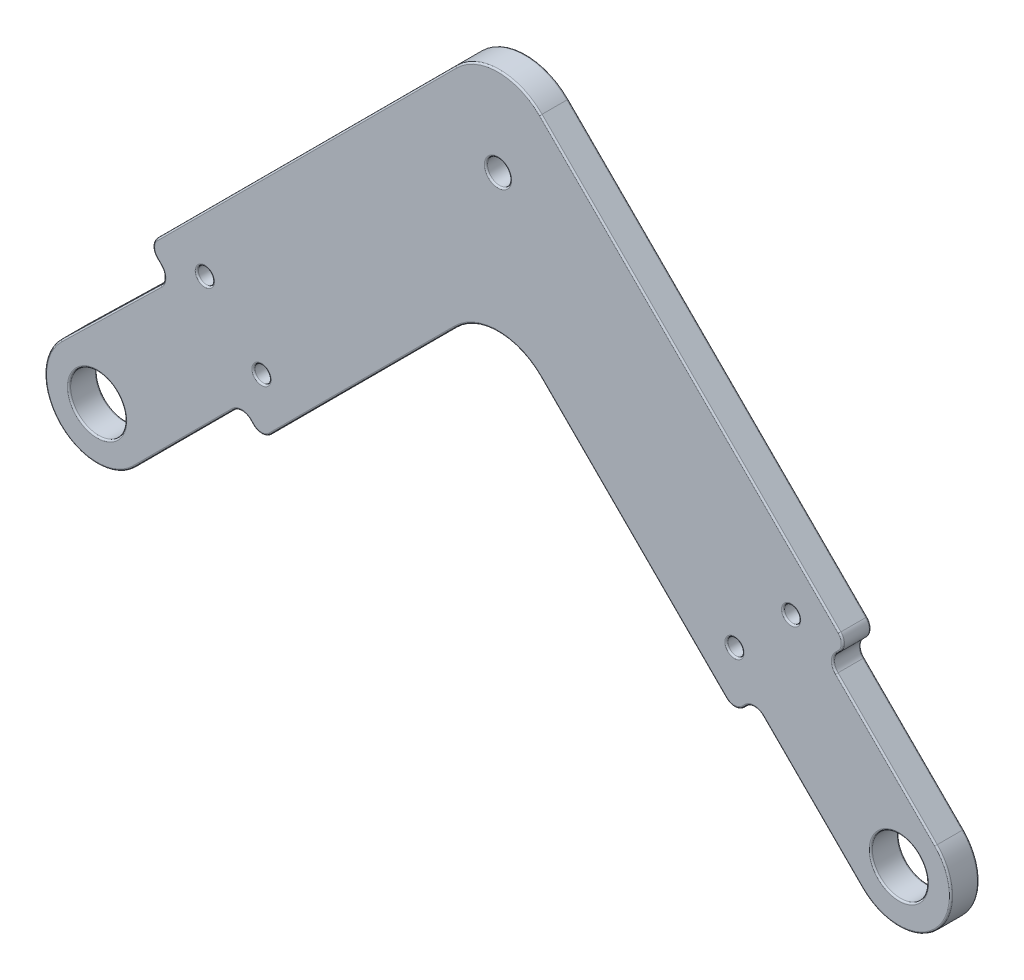
SolidWorks part; units mm, degrees
ref_plane "Front Plane" through (0, 0, 0) normal (0, 0, 1) x (1, 0, 0)
ref_plane "Top Plane" through (0, 0, 0) normal (0, 1, 0) x (1, 0, 0)
ref_plane "Right Plane" through (0, 0, 0) normal (1, 0, 0) x (0, 0, -1)
sketch "Sketch1" plane through (0, 0, 0) normal (0, 0, 1) x (1, 0, 0)
  line L0 (-100, 0) -> (100, 0) construction
  line L1 (-100, 0) -> (0, 100) construction
  line L2 (0, 100) -> (100, 0) construction
  line L3 (0, 0) -> (-50, 50) construction
  line L4 (-40, 60) -> (40, 60) construction
  line L5 (0, 100) -> (0, 60) construction
  circle A0 centre (-100, 0) radius 20
  circle A1 centre (0, 0) radius 20
  circle A2 centre (100, 0) radius 20
  point P2 (0, 0)
  dimension "D5" = 40
  dimension "D1" = 200
  dimension "D2" = 90
  dimension "D3" = 90
  dimension "D4" = 80
sketch "Sketch2" plane through (0, 0, 0) normal (0, 0, 1) x (1, 0, 0)
  line L0 (93.636, 20.5061) -> (79.4939, 6.364)
  line L1 (90.9809, 17.8509) -> (104.534, 4.6576)
  line L2 (-57.0711, 42.9289) -> (-40, 60) construction
  line L3 (-100, 0) -> (0, 100) construction
  line L4 (-40, 60) -> (40, 60) construction
  line L5 (40, 60) -> (86.565, 13.435) construction
  line L6 (0, 100) -> (100, 0) construction
  line L7 (-50, 35.8579) -> (-35.8579, 50)
  line L8 (-35.8579, 50) -> (35.8579, 50)
  line L9 (35.8579, 50) -> (79.4939, 6.364)
  line L10 (-64.1421, 50) -> (-44.1421, 70)
  line L11 (-44.1421, 70) -> (44.1421, 70)
  line L12 (44.1421, 70) -> (93.636, 20.5061)
  line L13 (-64.1421, 50) -> (-50, 35.8579)
  line L14 (82.1491, 9.0191) -> (95.3424, -4.534)
  line L15 (90.1005, 24.0416) -> (75.9584, 9.8995) construction
  line L17 (0, 100) -> (0, 60) construction
  line L18 (6, 70) -> (3.4304, 82.6944)
  line L19 (-6, 70) -> (-3.4304, 82.6944)
  circle A0 centre (100, 0) radius 3.5
  circle A1 centre (100, 0) radius 10 construction
  arc A2 (95.3424, -4.534) -> (104.534, 4.6576) centre (100, 0) ccw
  circle A3 centre (100, 0) radius 20 construction
  circle A4 centre (100, 0) radius 6.5 construction
  circle A5 centre (86.565, 20.5061) radius 1
  circle A6 centre (79.4939, 13.435) radius 1
  circle A7 centre (0, 60) radius 1.5
  circle A9 centre (0, 82) radius 1.5
  arc A10 (3.4304, 82.6944) -> (-3.4304, 82.6944) centre (0, 82) ccw
  circle A11 centre (0, 82) radius 3.5 construction
  circle A13 centre (-50, 50) radius 1.5
  dimension "D4" = 20
  dimension "D5" = 7
  dimension "D9" = 2
  dimension "D12" = 3
  dimension "D18" = 3
  dimension "D3" = 20
  dimension "D7" = 19
  dimension "D8" = 5
  dimension "D10" = 5
  dimension "D11" = 5
  dimension "D13" = 12
  dimension "D15" = 6
  dimension "D16" = 6
  dimension "D1" = 10
  dimension "D2" = 10
  dimension "D6" = 3
  dimension "D14" = 2
sketch "Sketch3" plane through (0, 0, 0) normal (0, 0, 1) x (1, 0, 0)
  line L0 (-86.565, 13.435) -> (-50, 50) construction
  line L1 (-100, 0) -> (0, 100) construction
  line L2 (-50, 50) -> (-13.435, 13.435) construction
  line L3 (0, 0) -> (-50, 50) construction
  line L4 (-79.4939, 6.364) -> (-50, 35.8579)
  line L5 (-50, 35.8579) -> (-20.5061, 6.364)
  line L6 (-93.636, 20.5061) -> (-50, 64.1421)
  line L7 (-50, 64.1421) -> (-6.364, 20.5061)
  line L8 (-79.4939, 6.364) -> (-50, 35.8579) construction
  line L9 (-93.636, 20.5061) -> (-50, 64.1421) construction
  line L10 (-93.636, 20.5061) -> (-79.4939, 6.364)
  line L11 (-6.364, 20.5061) -> (-20.5061, 6.364)
  line L12 (-104.534, 4.6576) -> (-90.9809, 17.8509)
  line L13 (-95.4038, -4.5962) -> (-81.9688, 8.8388)
  line L14 (4.5962, 4.5962) -> (-8.8388, 18.0312)
  line L15 (-4.5962, -4.5962) -> (-18.0312, 8.8388)
  line L16 (-90.1005, 24.0416) -> (-75.9584, 9.8995) construction
  line L17 (-9.8995, 24.0416) -> (-24.0416, 9.8995) construction
  circle A0 centre (-100, 0) radius 3.5
  circle A1 centre (0, 0) radius 3.5
  circle A2 centre (-100, 0) radius 10 construction
  circle A3 centre (0, 0) radius 10 construction
  arc A4 (-104.534, 4.6576) -> (-95.4038, -4.5962) centre (-100, 0) ccw
  arc A5 (-4.5962, -4.5962) -> (4.5962, 4.5962) centre (0, 0) ccw
  circle A6 centre (-100, 0) radius 20 construction
  circle A7 centre (-100, 0) radius 6.5 construction
  circle A8 centre (0, 0) radius 6.5 construction
  circle A9 centre (-86.565, 20.5061) radius 1
  circle A10 centre (-79.4939, 13.435) radius 1
  circle A11 centre (-20.5061, 13.435) radius 1
  circle A12 centre (-13.435, 20.5061) radius 1
  circle A13 centre (-50, 50) radius 1.5 construction
  circle A14 centre (-50, 50) radius 1.5
  dimension "D1" = 7
  dimension "D2" = 20
  dimension "D3" = 3
  dimension "D8" = 2
  dimension "D6" = 19
  dimension "D7" = 19
  dimension "D9" = 5
  dimension "D10" = 5
  dimension "D11" = 5
  dimension "D12" = 5
  dimension "D13" = 5
  dimension "D14" = 5
  dimension "D4" = 10
  dimension "D5" = 10
sketch "Sketch5" plane through (0, 0, 0) normal (0, 0, 1) x (1, 0, 0)
  line L6 (4, 60) -> (4, 70)
  line L7 (-4, 60) -> (-4, 70)
  line L10 (-57.5, 93.3579) -> (57.5, 93.3579)
  line L11 (57.5, 93.3579) -> (57.5, 83.3579)
  line L12 (57.5, 83.3579) -> (44.1421, 70)
  line L13 (44.1421, 70) -> (-44.1421, 70)
  line L14 (-44.1421, 70) -> (-57.5, 83.3579)
  line L15 (-57.5, 83.3579) -> (-57.5, 93.3579)
  line L16 (-22.5, 84.8579) -> (22.5, 84.8579) construction
  line L17 (-22.5, 89.3579) -> (22.5, 89.3579)
  line L18 (-22.5, 80.3579) -> (22.5, 80.3579)
  circle A0 centre (0, 60) radius 1.5 construction
  circle A1 centre (0, 60) radius 1.5
  arc A2 (-4, 60) -> (4, 60) centre (0, 60) ccw
  circle A3 centre (0, 60) radius 4 construction
  arc A4 (-22.5, 89.3579) -> (-22.5, 80.3579) centre (-22.5, 84.8579) ccw
  arc A5 (22.5, 80.3579) -> (22.5, 89.3579) centre (22.5, 84.8579) ccw
  point P2 (0, 93.3579)
  point P7 (0, 84.8579)
  dimension "D1" = 115
  dimension "D2" = 10
  dimension "D3" = 2.5
  dimension "D4" = 45
  dimension "D5" = 9
  dimension "D6" = 4
sketch "Sketch6" plane through (0, 0, 0) normal (0, 0, 1) x (1, 0, 0)
  line L0 (-95.4038, -4.5962) -> (-81.9688, 8.8388) construction
  line L1 (-104.534, 4.6576) -> (-90.9809, 17.8509) construction
  line L2 (4.5962, 4.5962) -> (-8.8388, 18.0312) construction
  line L3 (-4.5962, -4.5962) -> (-18.0312, 8.8388) construction
  line L4 (-95.4038, -4.5962) -> (-81.9688, 8.8388)
  line L5 (-104.534, 4.6576) -> (-90.9809, 17.8509)
  line L6 (-79.4939, 6.364) -> (-50, 35.8579)
  line L7 (-50, 35.8579) -> (-20.5061, 6.364)
  line L8 (-20.5061, 6.364) -> (-6.364, 20.5061)
  line L9 (-6.364, 20.5061) -> (-50, 64.1421)
  line L10 (-50, 64.1421) -> (-93.636, 20.5061)
  line L11 (-93.636, 20.5061) -> (-79.4939, 6.364)
  line L12 (-79.4939, 6.364) -> (-50, 35.8579)
  line L13 (-50, 35.8579) -> (-20.5061, 6.364)
  line L14 (-20.5061, 6.364) -> (-18.0312, 8.8388)
  line L15 (-6.364, 20.5061) -> (-50, 64.1421)
  line L16 (-50, 64.1421) -> (-93.636, 20.5061)
  line L17 (-93.636, 20.5061) -> (-90.9809, 17.8509)
  line L18 (4.5962, 4.5962) -> (-8.8388, 18.0312)
  line L19 (-4.5962, -4.5962) -> (-18.0312, 8.8388)
  line L20 (-81.9688, 8.8388) -> (-79.4939, 6.364)
  line L21 (-8.8388, 18.0312) -> (-6.364, 20.5061)
  arc A0 (-104.534, 4.6576) -> (-95.4038, -4.5962) centre (-100, 0) ccw construction
  circle A1 centre (0, 0) radius 3.5
  circle A2 centre (0, 0) radius 3.5
  circle A3 centre (-100, 0) radius 3.5
  circle A4 centre (-100, 0) radius 3.5
  circle A5 centre (-20.5061, 13.435) radius 1
  circle A6 centre (-20.5061, 13.435) radius 1
  circle A7 centre (-79.4939, 13.435) radius 1
  circle A8 centre (-79.4939, 13.435) radius 1
  circle A9 centre (-86.565, 20.5061) radius 1
  circle A10 centre (-86.565, 20.5061) radius 1
  circle A11 centre (-50, 50) radius 1.5
  circle A12 centre (-50, 50) radius 1.5
  circle A13 centre (-13.435, 20.5061) radius 1
  circle A14 centre (-13.435, 20.5061) radius 1
  arc A15 (-4.5962, -4.5962) -> (4.5962, 4.5962) centre (0, 0) ccw construction
  arc A16 (-104.534, 4.6576) -> (-95.4038, -4.5962) centre (-100, 0) ccw
  arc A17 (-4.5962, -4.5962) -> (4.5962, 4.5962) centre (0, 0) ccw
  dimension "D1" = 0
  dimension "D2" = 0
  dimension "D3" = 0
  dimension "D4" = 0
  dimension "D5" = 0
  dimension "D6" = 0
  dimension "D7" = 0
  dimension "D8" = 0
extrude "Boss-Extrude1" add sketch "Sketch6" along normal blind 3.5
fillet "Fillet1" radius 7.5 2 edges at (-50, 35.8579, 1.75) (-50, 64.1421, 1.75)
fillet "Fillet2" radius 1.5 8 edges at (-93.636, 20.5061, 1.75) (-90.9809, 17.8509, 1.75) (-79.4939, 6.364, 1.75) (-81.9688, 8.8388, 1.75) (-6.364, 20.5061, 1.75) (-8.8388, 18.0312, 1.75) (-18.0312, 8.8388, 1.75) (-20.5061, 6.364, 1.75)
fillet "Fillet3" radius 0.2 62 edges at (-12.435, 20.5061, 0) (-12.435, 20.5061, 3.5) (-48.5, 50, 0) (-48.5, 50, 3.5) (-85.565, 20.5061, 0) (-85.565, 20.5061, 3.5) (-78.4939, 13.435, 0) (-78.4939, 13.435, 3.5) (-19.5061, 13.435, 0) (-19.5061, 13.435, 3.5) (-96.5, 0, 0) (-96.5, 0, 3.5) (3.5, 0, 0) (3.5, 0, 3.5) (-80.7313, 7.6014, 0) (-66.8683, 18.9896, 0) (-33.1317, 18.9896, 0) (-19.2687, 7.6014, 0) (-10.7834, 1.591, 0) (4.5962, -4.5962, 0) (-1.591, 10.7834, 0) (-7.6014, 19.2687, 0) (-26.0607, 40.2028, 0) (-92.3156, 19.1857, 0) (-98.3021, 10.724, 0) (-104.627, -4.5652, 0) (-89.2166, 1.591, 0) (-80.7313, 7.6014, 3.5) (-66.8683, 18.9896, 3.5) (-33.1317, 18.9896, 3.5) (-19.2687, 7.6014, 3.5) (-10.7834, 1.591, 3.5) (4.5962, -4.5962, 3.5) (-1.591, 10.7834, 3.5) (-7.6014, 19.2687, 3.5) (-26.0607, 40.2028, 3.5) (-73.9393, 40.2028, 3.5) (-92.3156, 19.1857, 3.5) (-98.3021, 10.724, 3.5) (-104.627, -4.5652, 3.5) (-89.2166, 1.591, 3.5) (-50, 61.0355, 0) (-50, 61.0355, 3.5) (-50, 32.7513, 0) (-50, 32.7513, 3.5) (-20.5061, 6.9853, 0) (-6.9853, 20.5061, 0) (-79.4939, 6.9853, 0) (-93.0147, 20.5061, 0) (-20.5061, 6.9853, 3.5) (-6.9853, 20.5061, 3.5) (-79.4939, 6.9853, 3.5) (-93.0147, 20.5061, 3.5) (-91.6166, 17.8552, 0) (-91.6166, 17.8552, 3.5) (-81.9688, 8.2175, 0) (-81.9688, 8.2175, 3.5) (-8.2175, 18.0312, 0) (-8.2175, 18.0312, 3.5) (-18.0312, 8.2175, 0) (-18.0312, 8.2175, 3.5) (-73.9393, 40.2028, 0)
